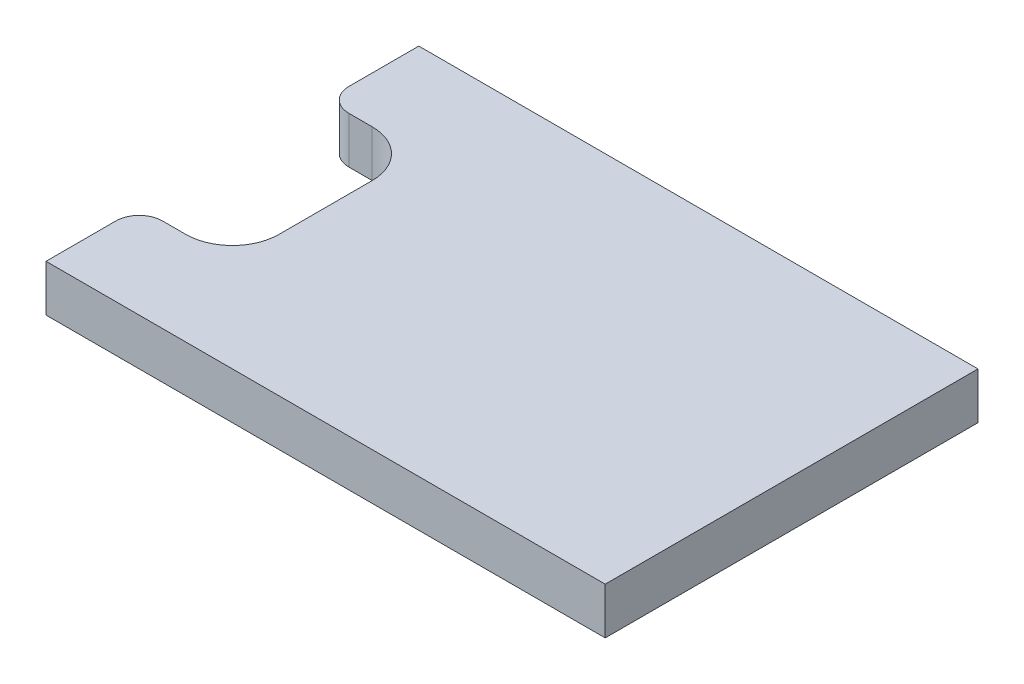
SolidWorks part; units mm, degrees
ref_plane "Front Plane" through (0, 0, 0) normal (0, 0, 1) x (1, 0, 0)
ref_plane "Top Plane" through (0, 0, 0) normal (0, 1, 0) x (1, 0, 0)
ref_plane "Right Plane" through (0, 0, 0) normal (1, 0, 0) x (0, 0, -1)
sketch "Sketch1" plane through (0, -150, 0) normal (0, -1, 0) x (1, 0, 0)
  line L1 (-86.4895, 26.9213) -> (33.5105, 26.9213)
  line L2 (-86.4895, 26.9213) -> (-86.4895, -53.0787)
  line L3 (-86.4895, -53.0787) -> (33.5105, -53.0787)
  line L4 (33.5105, 26.9213) -> (33.5105, -53.0787)
  dimension "D1" = 80
  dimension "D2" = 120
extrude "Boss-Extrude1" add sketch "Sketch1" along normal blind 10
sketch "Sketch2" plane through (0, -150, 0) normal (0, 1, 0) x (1, 0, 0)
  line L0 (-86.4895, -26.9213) -> (-86.4895, 53.0787) construction
  line L1 (-86.4895, 33.0787) -> (-66.4895, 33.0787)
  line L2 (-86.4895, 33.0787) -> (-86.4895, -6.9213)
  line L3 (-86.4895, -6.9213) -> (-66.4895, -6.9213)
  line L4 (-66.4895, 33.0787) -> (-66.4895, -6.9213)
  line L5 (-86.4895, 53.0787) -> (33.5105, 53.0787) construction
  line L6 (33.5105, -26.9213) -> (-86.4895, -26.9213) construction
  dimension "D1" = 20
  dimension "D2" = 20
  dimension "D3" = 20
extrude "Cut-Extrude1" cut sketch "Sketch2" against normal through all
fillet "Fillet1" radius 10 2 edges at (-66.4895, -155, 6.9213) (-66.4895, -155, -33.0787)
fillet "Fillet2" radius 5 2 edges at (-86.4895, -155, 6.9213) (-86.4895, -155, -33.0787)
